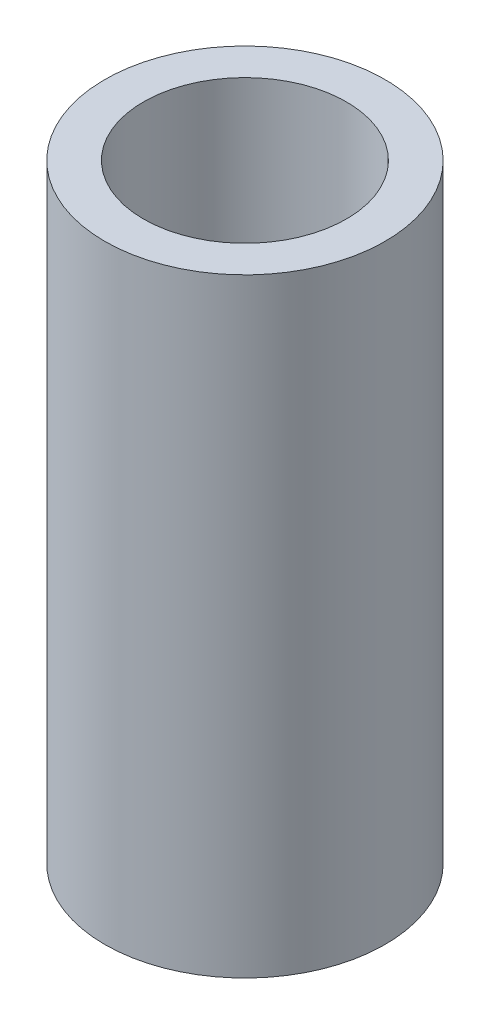
SolidWorks part; units mm, degrees
ref_plane "Plano frontal" through (0, 0, 0) normal (0, 0, 1) x (1, 0, 0)
ref_plane "Plano superior" through (0, 0, 0) normal (0, 1, 0) x (1, 0, 0)
ref_plane "Plano direito" through (0, 0, 0) normal (1, 0, 0) x (0, 0, -1)
sketch "Esboço1" plane through (0, 0, 0) normal (0, 1, 0) x (1, 0, 0)
  circle A0 centre (0, 0) radius 29
  circle A1 centre (0, 0) radius 21
  dimension "D1" = 42
  dimension "D2" = 58
extrude "Ressalto-extrusão1" add sketch "Esboço1" along normal mid plane 126
